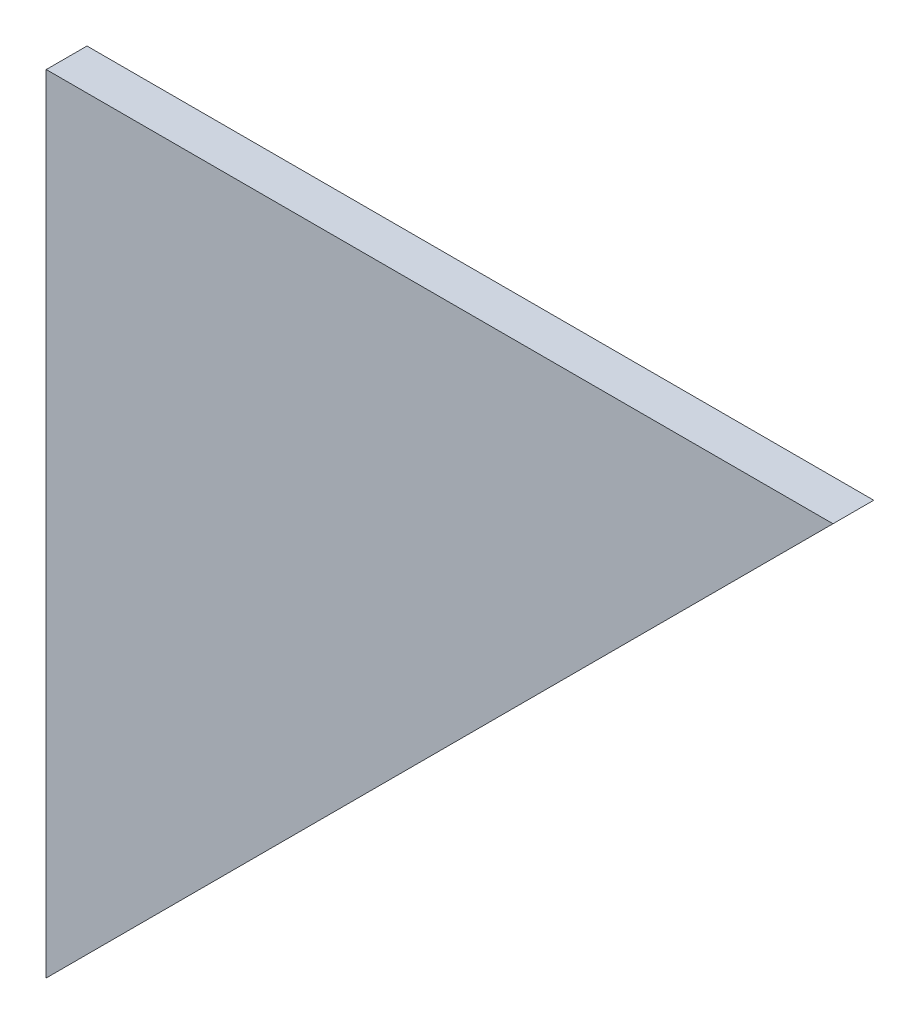
SolidWorks part; units mm, degrees
material "Acrylic (Medium-high impact)"
ref_plane "Front Plane" through (0, 0, 0) normal (0, 0, 1) x (1, 0, 0)
ref_plane "Top Plane" through (0, 0, 0) normal (0, 1, 0) x (1, 0, 0)
ref_plane "Right Plane" through (0, 0, 0) normal (1, 0, 0) x (0, 0, -1)
ref_plane "Plane1" through (0, 0, 113.7049) normal (0, 0, 1) x (1, 0, 0)
sketch "Sketch1" plane through (0, 0, 113.7049) normal (0, 0, 1) x (1, 0, 0)
  line L0 (49.6381, -107.5728) -> (107.5728, -49.6381) construction
  line L1 (107.5728, -49.6381) -> (49.6381, -49.6381) construction
  line L2 (49.6381, -49.6381) -> (49.6381, -107.5728) construction
  line L3 (49.6381, -107.5728) -> (107.5728, -49.6381)
  line L4 (107.5728, -49.6381) -> (49.6381, -49.6381)
  line L5 (49.6381, -49.6381) -> (49.6381, -107.5728)
extrude "Boss-Extrude1" add sketch "Sketch1" along normal mid plane 3
